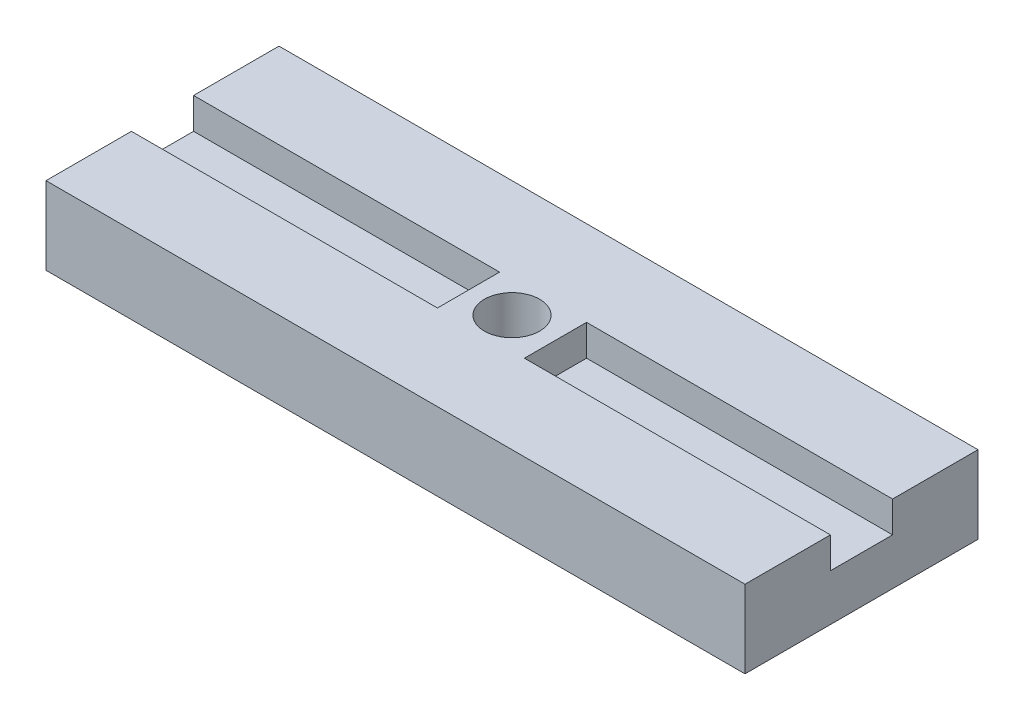
SolidWorks part; units mm, degrees
ref_plane "Front Plane" through (0, 0, 0) normal (0, 0, 1) x (1, 0, 0)
ref_plane "Top Plane" through (0, 0, 0) normal (0, 1, 0) x (1, 0, 0)
ref_plane "Right Plane" through (0, 0, 0) normal (1, 0, 0) x (0, 0, -1)
sketch "Sketch1" plane through (0, 0, 0) normal (0, 1, 0) x (1, 0, 0)
  line L1 (-14.2875, -4.7625) -> (14.2875, -4.7625)
  line L2 (-14.2875, -4.7625) -> (-14.2875, 4.7625)
  line L3 (-14.2875, 4.7625) -> (14.2875, 4.7625)
  line L4 (14.2875, -4.7625) -> (14.2875, 4.7625)
  line L5 (-14.2875, -4.7625) -> (14.2875, 4.7625) construction
  line L6 (-14.2875, 4.7625) -> (14.2875, -4.7625) construction
  point P0 (0, 0)
  dimension "D1" = 28.575
  dimension "D2" = 9.525
extrude "Boss-Extrude1" add sketch "Sketch1" along normal blind 3.175
hole_wizard "#4-40 Tapped Hole1" positions "Sketch3" profile "Sketch4" tap size "#4-40" standard "ANSI Inch"
sketch "Sketch3" plane through (0, 3.175, 0) normal (0, 1, 0) x (1, 0, 0)
  point P0 (0, 0)
sketch "Sketch4" plane through (0, 3.175, 0) normal (1, 0, 0) x (0, 0, 1)
  line L0 (0, 0) -> (0, 8.2738)
  line L1 (0, 8.2738) -> (1.1303, 7.5946)
  line L2 (1.1303, 7.5946) -> (1.1303, 0)
  line L5 (1.1303, 0) -> (0, 0)
  line L10 (0, 8.2738) -> (-1.1303, 7.5946) construction
  line L11 (0, -6.35) -> (0, 107.95) construction
  dimension "Tap Drill Dia." = 2.2606
  dimension "Tap Drill Depth" = 7.5946
  dimension "Drill Angle" = 118
cosmetic thread "Hole Thread1" parameters "D1"=5.6896, "D2"=2.8448
sketch "Sketch5" plane through (0, 3.175, 0) normal (0, 1, 0) x (1, 0, 0)
  line L0 (-14.2875, 4.7625) -> (-14.2875, -4.7625) construction
  line L1 (-14.2875, -1.27) -> (-1.778, -1.27)
  line L2 (-14.2875, -1.27) -> (-14.2875, 1.27)
  line L3 (-14.2875, 1.27) -> (-1.778, 1.27)
  line L4 (-1.778, -1.27) -> (-1.778, 1.27)
  line L5 (-14.2875, -1.27) -> (-1.778, 1.27) construction
  line L6 (-14.2875, 1.27) -> (-1.778, -1.27) construction
  line L7 (0, 0) -> (0, 4.7625) construction
  line L8 (14.2875, 4.7625) -> (-14.2875, 4.7625) construction
  line L9 (14.2875, 1.27) -> (1.778, -1.27) construction
  line L10 (14.2875, -1.27) -> (1.778, 1.27) construction
  line L11 (1.778, -1.27) -> (1.778, 1.27)
  line L12 (14.2875, 1.27) -> (1.778, 1.27)
  line L13 (14.2875, -1.27) -> (14.2875, 1.27)
  line L14 (14.2875, -1.27) -> (1.778, -1.27)
  point P0 (-8.0328, 0)
  point P17 (8.0328, 0)
  dimension "D1" = 1.778
  dimension "D2" = 2.54
extrude "Cut-Extrude2" cut sketch "Sketch5" against normal blind 1.27
